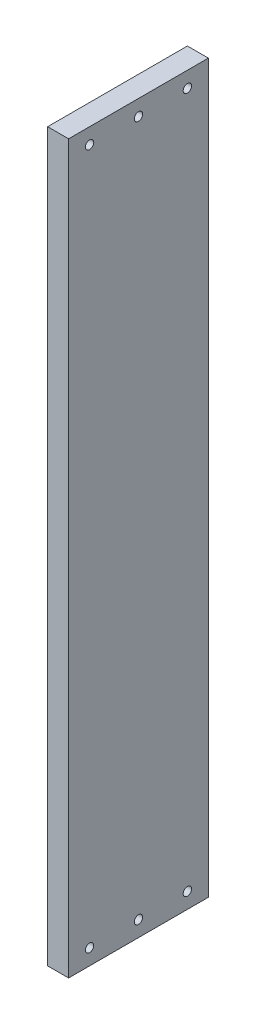
SolidWorks part; units mm, degrees
ref_plane "Front Plane" through (0, 0, 0) normal (0, 0, 1) x (1, 0, 0)
ref_plane "Top Plane" through (0, 0, 0) normal (0, 1, 0) x (1, 0, 0)
ref_plane "Right Plane" through (0, 0, 0) normal (1, 0, 0) x (0, 0, -1)
sketch "Sketch1" plane through (0, 0, 0) normal (0, 1, 0) x (1, 0, 0)
  line L1 (0, 0) -> (19.05, 0)
  line L2 (0, 0) -> (0, 127)
  line L3 (0, 127) -> (19.05, 127)
  line L4 (19.05, 0) -> (19.05, 127)
  dimension "D1" = 19.05
  dimension "D2" = 127
extrude "Boss-Extrude1" add sketch "Sketch1" along normal blind 660.4
sketch "Sketch2" plane through (19.05, 0, 0) normal (1, 0, 0) x (0, 0, -1)
  line L0 (0, 660.4) -> (127, 660.4) construction
  line L2 (0, 660.4) -> (0, 0) construction
  line L3 (127, 660.4) -> (127, 0) construction
  line L4 (127, 330.2) -> (0, 330.2) construction
  circle A0 centre (107.95, 646.176) radius 3.81
  circle A1 centre (63.5, 646.176) radius 3.81
  circle A2 centre (19.05, 646.176) radius 3.81
  circle A6 centre (19.05, 14.224) radius 3.81
  circle A7 centre (63.5, 14.224) radius 3.81
  circle A8 centre (107.95, 14.224) radius 3.81
  dimension "D2" = 7.62
  dimension "D3" = 7.62
  dimension "D4" = 7.62
  dimension "D8" = 19.05
  dimension "D1" = 14.224
  dimension "D5" = 44.45
  dimension "D6" = 14.224
  dimension "D7" = 14.224
  dimension "D9" = 19.05
extrude "Cut-Extrude1" cut sketch "Sketch2" against normal blind 37.846
equation "\"LengthOfShort\"= \"length desired@Drivetrain.SLDASM\""
equation "\"D1@Boss-Extrude1\"=\"LengthOfShort\""
